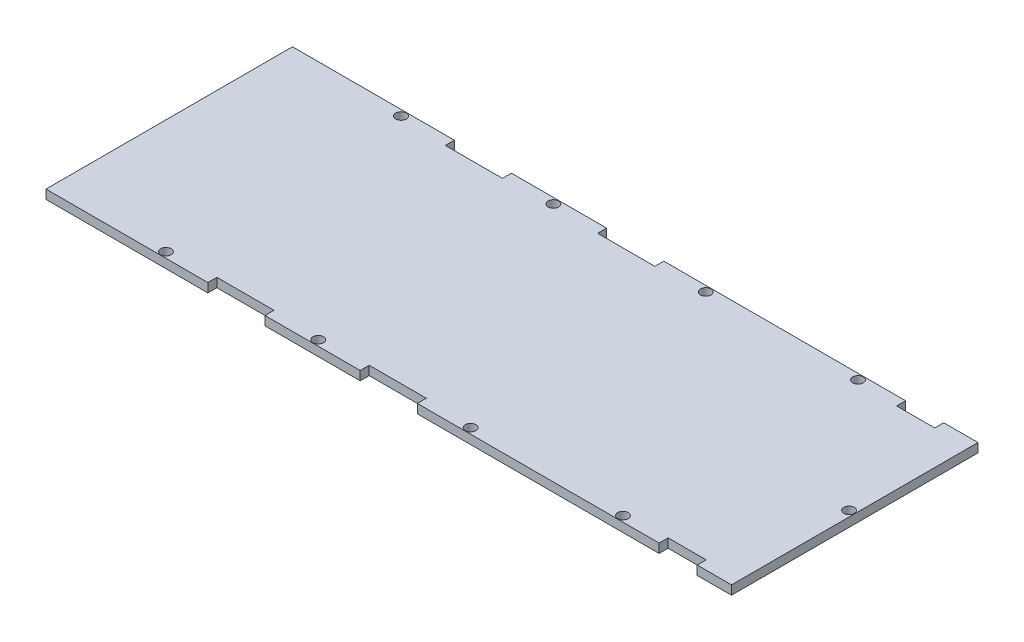
SolidWorks part; units mm, degrees
ref_plane "Front Plane" through (0, 0, 0) normal (0, 0, 1) x (1, 0, 0)
ref_plane "Top Plane" through (0, 0, 0) normal (0, 1, 0) x (1, 0, 0)
ref_plane "Right Plane" through (0, 0, 0) normal (1, 0, 0) x (0, 0, -1)
sketch "Sketch1" plane through (0, 0, 0) normal (0, 1, 0) x (1, 0, 0)
  line L0 (114.3, -0.8322) -> (114.3, -41.1)
  line L1 (-114.3, 41.1) -> (-77.5289, 41.1)
  line L2 (-114.3, 41.1) -> (-114.3, -41.1)
  line L3 (-114.3, -41.1) -> (-77.5289, -41.1)
  line L4 (114.3, 41.1) -> (114.3, 1.1822)
  line L5 (-74.8711, 41.1) -> (-60.325, 41.1)
  line L6 (26.7289, 41.1) -> (74.8711, 41.1)
  line L7 (77.5289, 41.1) -> (89.4932, 41.1)
  line L8 (-24.0711, 41.1) -> (-9.525, 41.1)
  line L9 (-119.8539, 0) -> (200.76, 0) construction
  line L10 (77.5289, -41.1) -> (89.4932, -41.1)
  line L11 (26.7289, -41.1) -> (74.8711, -41.1)
  line L12 (-24.0711, -41.1) -> (-9.525, -41.1)
  line L13 (-74.8711, -41.1) -> (-60.325, -41.1)
  line L14 (-41.275, -41.1) -> (-26.7289, -41.1)
  line L15 (9.525, -41.1) -> (24.0711, -41.1)
  line L16 (-60.325, -41.1) -> (-60.325, -38.1)
  line L17 (-60.325, -38.1) -> (-41.275, -38.1)
  line L18 (-41.275, -41.1) -> (-41.275, -38.1)
  line L19 (-60.325, -43.7685) -> (-41.275, -38.1) construction
  line L20 (-60.325, -38.1) -> (-41.275, -43.7685) construction
  line L21 (102.87, -41.1) -> (114.3, -41.1)
  line L22 (-9.525, -41.1) -> (-9.525, -38.1)
  line L23 (-9.525, -38.1) -> (9.525, -38.1)
  line L24 (9.525, -41.1) -> (9.525, -38.1)
  line L25 (-9.525, -43.7685) -> (9.525, -38.1) construction
  line L26 (-9.525, -38.1) -> (9.525, -43.7685) construction
  line L27 (102.87, 41.1) -> (102.87, 38.1)
  line L28 (89.4932, 41.1) -> (90.17, 41.1)
  line L29 (102.87, 38.1) -> (90.17, 38.1)
  line L30 (102.87, -41.1) -> (102.87, -38.1)
  line L31 (102.87, -38.1) -> (90.17, -38.1)
  line L32 (90.17, -41.1) -> (90.17, -38.1)
  line L33 (90.17, 41.1) -> (90.17, 38.1)
  line L34 (-77.5289, -41.1) -> (-74.8711, -41.1)
  line L35 (9.525, 41.1) -> (9.525, 38.1)
  line L36 (-9.525, 38.1) -> (9.525, 38.1)
  line L37 (-9.525, 41.1) -> (-9.525, 38.1)
  line L38 (-41.275, 41.1) -> (-41.275, 38.1)
  line L39 (-60.325, 38.1) -> (-41.275, 38.1)
  line L40 (-60.325, 41.1) -> (-60.325, 38.1)
  line L41 (-41.275, 41.1) -> (-26.7289, 41.1)
  line L42 (9.525, 41.1) -> (24.0711, 41.1)
  line L43 (102.87, 41.1) -> (114.3, 41.1)
  line L44 (89.4932, -41.1) -> (90.17, -41.1)
  line L45 (-77.5289, 41.1) -> (-74.8711, 41.1)
  line L46 (-26.7289, 41.1) -> (-24.0711, 41.1)
  line L47 (24.0711, 41.1) -> (26.7289, 41.1)
  line L48 (74.8711, 41.1) -> (77.5289, 41.1)
  line L49 (114.3, 1.1822) -> (114.3, -0.8322)
  line L50 (74.8711, -41.1) -> (77.5289, -41.1)
  line L51 (24.0711, -41.1) -> (26.7289, -41.1)
  line L52 (-26.7289, -41.1) -> (-24.0711, -41.1)
  circle A0 centre (-25.4, -39.195) radius 1.7526
  circle A1 centre (112.395, 0) radius 1.7526
  circle A2 centre (25.4, -39.195) radius 1.7526
  circle A3 centre (76.2, -39.195) radius 1.7526
  circle A4 centre (76.2, 39.195) radius 1.7526
  circle A5 centre (25.4, 39.195) radius 1.7526
  circle A6 centre (-25.4, 39.195) radius 1.7526
  circle A7 centre (-76.2, 39.195) radius 1.7526
  circle A9 centre (-76.2, -39.195) radius 1.7526
  point P34 (-50.8, -40.9342)
  point P39 (0, -40.9342)
  dimension "D5" = 1.905
  dimension "D6" = 3.5052
  dimension "D7" = 3.5052
  dimension "D15" = 1.905
  dimension "D8" = 3.5052
  dimension "D18" = 1.905
  dimension "D1" = 228.6
  dimension "D2" = 114.3
  dimension "D3" = 3
  dimension "D4" = 82.2
  dimension "D9" = 19.05
  dimension "D10" = 19.05
  dimension "D11" = 11.43
  dimension "D12" = 3
  dimension "D13" = 3
  dimension "D14" = 12.7
  dimension "D16" = 1.905
  dimension "D17" = 1.905
extrude "Boss-Extrude1" add sketch "Sketch1" along normal blind 3
